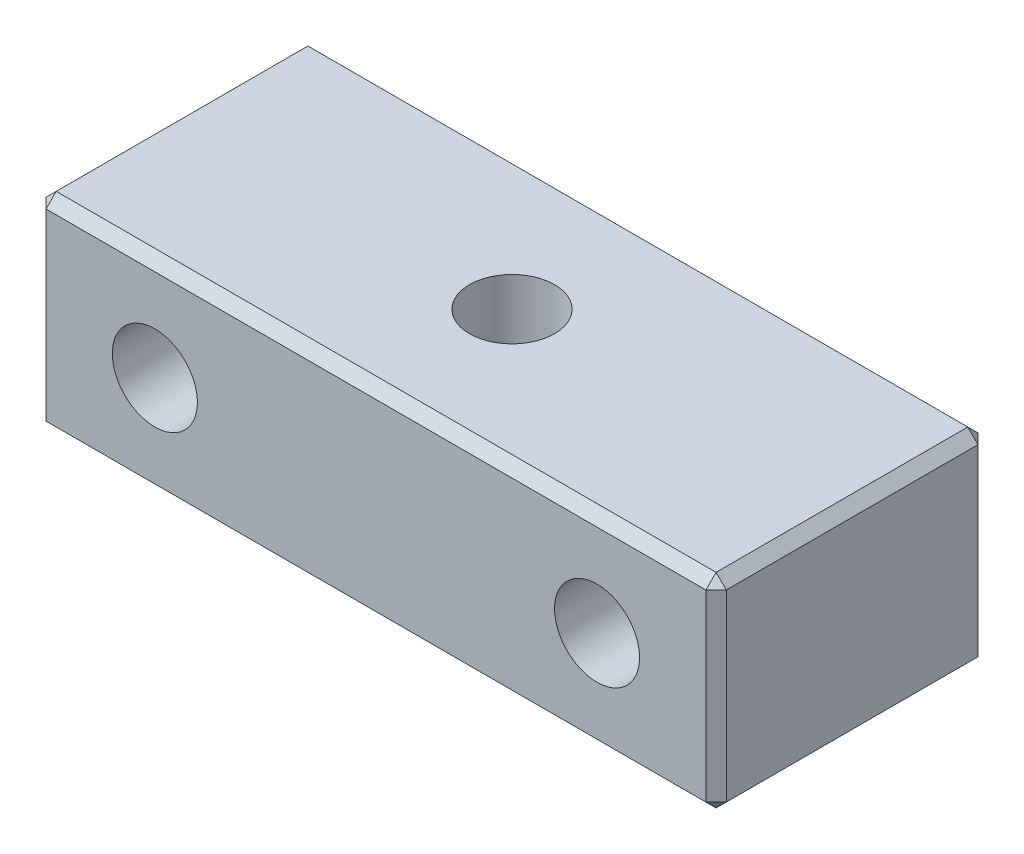
SolidWorks part; units mm, degrees
material "1060 合金"
ref_plane "前视基准面" through (0, 0, 0) normal (0, 0, 1) x (1, 0, 0)
ref_plane "上视基准面" through (0, 0, 0) normal (0, 1, 0) x (1, 0, 0)
ref_plane "右视基准面" through (0, 0, 0) normal (1, 0, 0) x (0, 0, -1)
other "Configuration Table"
sketch "草图1" plane through (0, 0, 0) normal (0, 1, 0) x (1, 0, 0)
  line L1 (-10, -4) -> (10, -4)
  line L2 (-10, -4) -> (-10, 4)
  line L3 (-10, 4) -> (10, 4)
  line L4 (10, -4) -> (10, 4)
  line L5 (-10, -4) -> (10, 4) construction
  line L6 (-10, 4) -> (10, -4) construction
  point P0 (0, 0)
  dimension "D1" = 20
  dimension "D2" = 8
extrude "凸台-拉伸1" add sketch "草图1" along normal blind 6
sketch "草图2" plane through (0, 0, -4) normal (0, 0, -1) x (-1, 0, 0)
  line L0 (0, 0) -> (0, 6) construction
  line L1 (-10, 0) -> (10, 0) construction
  line L2 (-10, 6) -> (10, 6) construction
  circle A0 centre (-6.5, 3) radius 1.525
  circle A1 centre (6.5, 3) radius 1.525
  point P4 (0, 3)
  dimension "D1" = 3.05
  dimension "D2" = 13
hole_wizard "M3 螺纹孔1" positions "3D草图2" profile "草图4" tap size "M3" standard "GB" end condition through all
sketch3d "3D草图2"
  point P0 (6.5, 3, -4)
  point P3 (-6.5, 3, -4)
sketch "草图4" plane through (6.5, 3, -4) normal (1, 0, 0) x (0, 1, 0)
  line L0 (0, 0) -> (0, 8)
  line L1 (0, 8) -> (1.25, 8)
  line L2 (1.25, 8) -> (1.25, 0)
  line L5 (1.25, 0) -> (0, 0)
  line L11 (0, -6.35) -> (0, 107.95) construction
  dimension "通孔螺纹孔钻头直径" = 2.5
  dimension "通孔螺纹孔钻头深度" = 8
cosmetic thread "孔螺蚊线1" parameters "D2"=3
cosmetic thread "孔螺蚊线2" parameters "D2"=3
sketch "草图9" plane through (0, 6, 0) normal (0, 1, 0) x (1, 0, 0)
  circle A0 centre (0, 0) radius 1.5
  dimension "D1" = 3
hole_wizard "M3 螺纹孔2" positions "3D草图5" profile "草图10" tap size "M3" standard "GB" end condition through all
sketch3d "3D草图5"
  point P0 (0, 6, 0)
sketch "草图10" plane through (0, 6, 0) normal (1, 0, 0) x (0, 0, 1)
  line L0 (0, 0) -> (0, 6)
  line L1 (0, 6) -> (1.25, 6)
  line L2 (1.25, 6) -> (1.25, 0)
  line L5 (1.25, 0) -> (0, 0)
  line L11 (0, -6.35) -> (0, 107.95) construction
  dimension "通孔螺纹孔钻头直径" = 2.5
  dimension "通孔螺纹孔钻头深度" = 6
cosmetic thread "孔螺蚊线3" parameters "D2"=3
chamfer "倒角1" distance 0.3 angle 45 12 edges at (10, 3, 4) (10, 6, 0) (10, 3, -4) (10, 0, 0) (-10, 3, -4) (0, 0, -4) (-10, 0, 0) (0, 0, 4) (-10, 3, 4) (0, 6, 4) (-10, 6, 0) (0, 6, -4)
